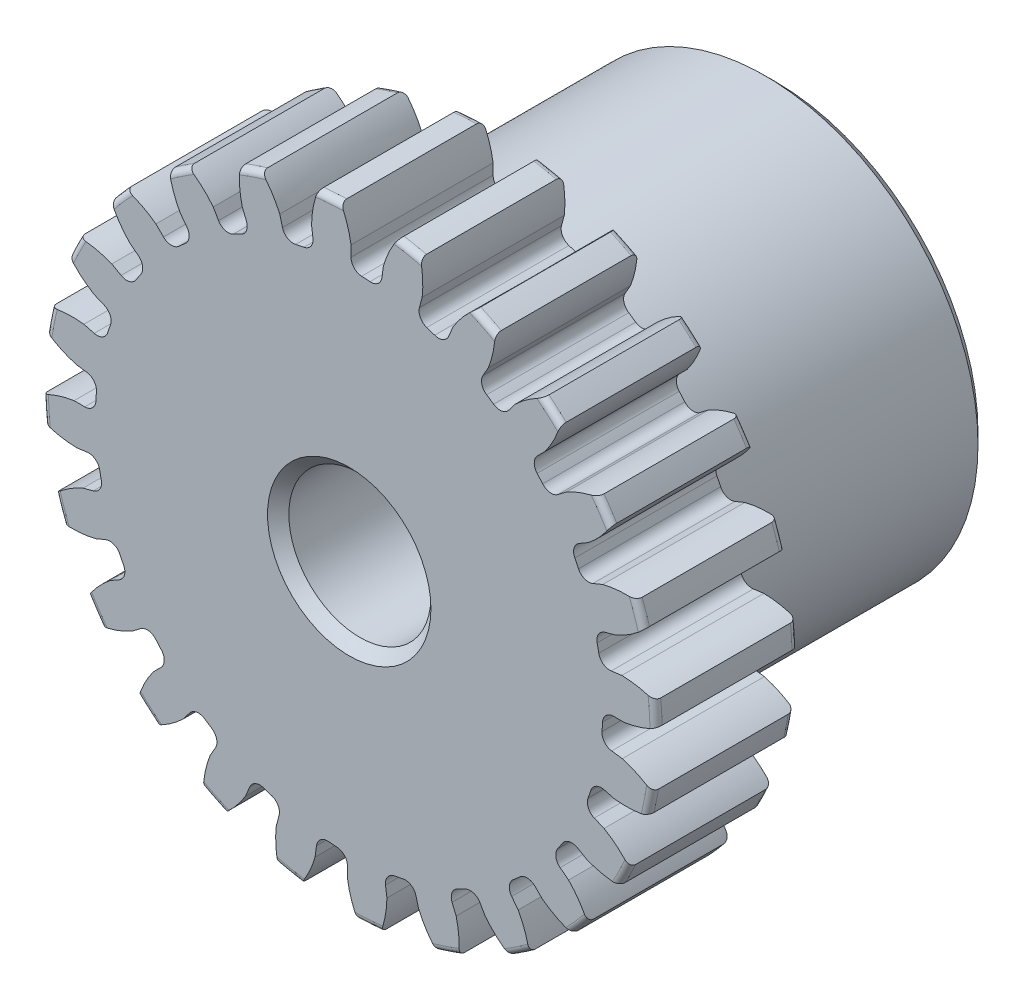
SolidWorks part; units mm, degrees
ref_plane "Front" through (0, 0, 0) normal (0, 0, 1) x (1, 0, 0)
ref_plane "Top" through (0, 0, 0) normal (0, 1, 0) x (1, 0, 0)
ref_plane "Right" through (0, 0, 0) normal (1, 0, 0) x (0, 0, -1)
sketch "Sketch1" plane through (0, 0, 0) normal (0, 0, 1) x (1, 0, 0)
  line L0 (-304.8, 0) -> (304.8, 0) construction
  circle A0 centre (0, 0) radius 6.858
  circle A1 centre (0, 0) radius 6.35 construction
  circle A3 centre (0, 0) radius 5.6674 construction
  dimension "D1" = 1.1906
  dimension "OD" = 13.716
  dimension "Ptich Dia" = 12.7
  dimension "Root Dia" = 11.3348
  dimension "D3" = 0.508
  dimension "Number of Teeth" = 609.6
extrude "Boss-Extrude1" add sketch "Sketch1" against normal blind 3.175
sketch "Sketch2" plane through (0, 0, 0) normal (1, 0, 0) x (0, 0, -1)
  line L0 (3.175, 0) -> (9.525, 0)
  line L1 (3.175, 0) -> (3.175, 4.7625)
  line L2 (3.175, 4.7625) -> (9.525, 4.7625)
  line L3 (9.525, 4.7625) -> (9.525, 0)
  point P5 (9.525, -4.7625)
  point P6 (0, -6.858)
  point P7 (3.175, -6.858)
  point P9 (0, 6.858)
  dimension "Face Wd" = 3.175
  dimension "B Hub Dia" = 9.525
  dimension "D O'all Lg." = 9.525
revolve "Revolve1" add sketch "Sketch2" angle 360 about L0
fillet "Fillet2" radius 0.1372 3 edges at (6.858, 0, -3.175) (6.858, 0, 0) (4.7625, 0, -3.175)
sketch "Sketch3" plane through (0, 0, 0) normal (0, 0, 1) x (1, 0, 0)
  line L0 (0, 0) -> (0, 6.858) construction
  line L1 (-1.5393, 5.9519) -> (0, 6.35)
  line L2 (-9.5921, 6.35) -> (9.5921, 6.35) construction
  line L3 (-9.2865, 3.9483) -> (9.2865, 8.7517) construction
  line L4 (-1.5393, 5.9519) -> (0, 0) construction
  line L5 (-3.9262, 4.7307) -> (0, 0) construction
  line L6 (-3.9262, 4.7307) -> (-0.6424, 7.456) construction
  line L7 (-1.0733, 6.0533) -> (0, 0) construction
  line L8 (-1.0733, 6.0533) -> (0.0225, 6.2476) construction
  arc A0 (-1.5393, 5.9519) -> (-3.9262, 4.7307) centre (0, 0) ccw
  circle A1 centre (0, 0) radius 6.35 construction
  circle A2 centre (0, 0) radius 6.1477 construction
  arc A3 (-1.5393, 5.9519) -> (-1.0733, 6.0533) centre (0, 0) cw
  circle A4 centre (0, 0) radius 6.858 construction
  point P6 (0, 6.35)
  dimension "D1" = 1.5899
  dimension "Pressure Angle" = 14.5
  dimension "D2" = 2.7029
  dimension "D3" = 4.2674
  dimension "D4" = 0.477
  dimension "D5" = 1.1129
sketch "Sketch4" plane through (0, 0, 0) normal (0, 0, 1) x (1, 0, 0)
  line L0 (0, 0) -> (0.4144, 6.3228) construction
  line L1 (0.0398, 6.1476) -> (0.0398, 5.6672)
  line L2 (0, 6.35) -> (0.8288, 6.2957) construction
  line L3 (0.763, 6.1002) -> (0.7003, 5.6239)
  line L4 (0.0398, 5.6672) -> (0, 0) construction
  line L5 (0, 0) -> (0, 6.858) construction
  line L6 (-3.9262, 4.7307) -> (-0.6424, 7.456) construction
  line L7 (-3.9262, 4.7307) -> (-0.6424, 7.456) construction
  arc A0 (0.7003, 5.6239) -> (0.0398, 5.6672) centre (0, 0) ccw
  arc A1 (0, 6.35) -> (0.8288, 6.2957) centre (0, 0) cw construction
  circle A2 centre (0, 0) radius 6.35 construction
  circle A3 centre (0, 0) radius 6.1477 construction
  circle A4 centre (0, 0) radius 5.6674 construction
  arc A5 (1.6101, 7.3084) -> (-0.6424, 7.456) centre (0, 0) ccw
  spline S0 degree 2 poles (-0.6424, 7.456) (-0.0701, 6.8828) (0.0398, 6.1476) knots 0 0 0 1 1 1
  spline S1 degree 2 poles (1.6101, 7.3084) (0.9679, 6.8147) (0.763, 6.1002) knots 0 0 0 1 1 1
  dimension "D1" = 0.8312
extrude "Cut-Extrude1" cut sketch "Sketch4" against normal through all
fillet "Fillet1" radius 0.2494 2 edges at (0.7003, 5.6239, -1.5875) (0.0398, 5.6672, -1.5875)
pattern_circular "CirPattern1" count 24 over 360 about axis through (0, 0, -3.175) along (0, 0, 1) of "Cut-Extrude1", "Fillet1"
sketch "Sketch5" plane through (0, 0, 0) normal (0, 0, 1) x (1, 0, 0)
  circle A0 centre (0, 0) radius 1.5875
  circle A1 centre (0, 0) radius 1.5875 construction
  dimension "Bore Min" = 3.175
  dimension "Bore Max" = 3.175
extrude "Cut-Extrude2" cut sketch "Sketch5" against normal through all
chamfer "Chamfer1" distance 0.2381 angle 45 3 edges at (4.7625, 0, -9.525) (1.5875, 0, 0) (1.5875, 0, -9.525)
sketch "Pitch Dia" plane through (0, 0, 0) normal (0, 0, 1) x (1, 0, 0)
  circle A0 centre (0, 0) radius 6.35 construction
  circle A1 centre (0, 0) radius 6.35 construction
equation "\"D1@Boss-Extrude1\" = \"Face Wd@Sketch2\""
equation "\"D2@Sketch3\" = \"D1@Sketch3\"*1.7"
equation "\"D3@Sketch3\" = \"D1@Sketch3\"+\"D2@Sketch3\"-.001"
equation "\"D4@Sketch3\" = \"D1@Sketch3\"*.3"
equation "\"D5@Sketch3\" = \"D1@Sketch3\"-\"D4@Sketch3\""
equation "\"D1@Sketch4\" = 1.5708/(\"Number of Teeth@Sketch1\"/\"Ptich Dia@Sketch1\")"
equation "\"D1@Chamfer1\" = \"B Hub Dia@Sketch2\"*.025"
equation "\"D1@CirPattern1\" = \"Number of Teeth@Sketch1\""
equation "\"D1@Fillet1\" = \"D1@Sketch4\"*.3"
equation "\"D1@Fillet2\" = \"OD@Sketch1\"*.01"
equation "\"D1@Sketch1\" = 2.250/(\"Number of Teeth@Sketch1\"/\"Ptich Dia@Sketch1\")"
